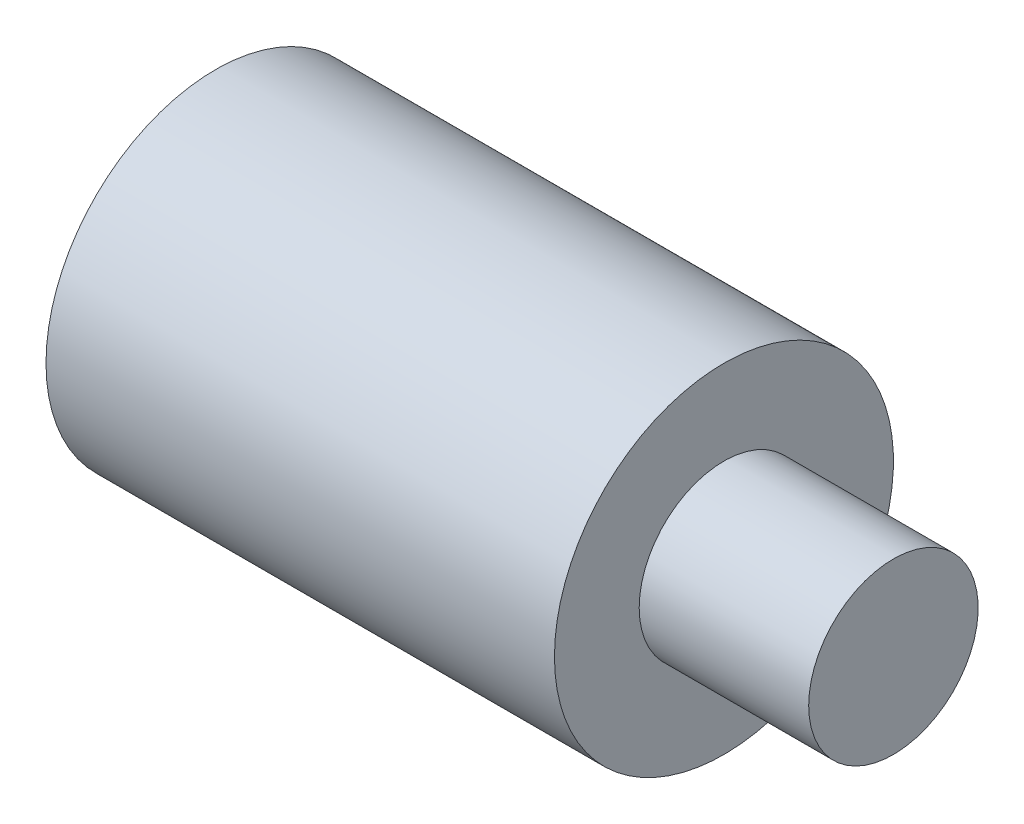
SolidWorks part; units mm, degrees
ref_plane "Front Plane" through (0, 0, 0) normal (0, 0, 1) x (1, 0, 0)
ref_plane "Top Plane" through (0, 0, 0) normal (0, 1, 0) x (1, 0, 0)
ref_plane "Right Plane" through (0, 0, 0) normal (1, 0, 0) x (0, 0, -1)
sketch "Sketch1" plane through (0, 0, 0) normal (0, 0, 1) x (1, 0, 0)
  line L0 (-27.5667, 0) -> (25.4, 0) construction
  line L1 (0, 0) -> (0, 6.35)
  line L2 (0, 6.35) -> (19.05, 6.35)
  line L3 (19.05, 6.35) -> (19.05, 3.175)
  line L4 (19.05, 3.175) -> (25.4, 3.175)
  line L6 (25.4, 0) -> (0, 0)
  line L8 (25.4, 3.175) -> (25.4, 0)
  point P8 (35.4, 3.175)
  point P9 (60.4702, 6.35)
  point P10 (22.6007, 6.35)
  dimension "D4" = 25.4
  dimension "D1" = 12.7
  dimension "D2" = 6.35
  dimension "D5" = 6.35
revolve "Revolve1" add sketch "Sketch1" angle 360 about L0
